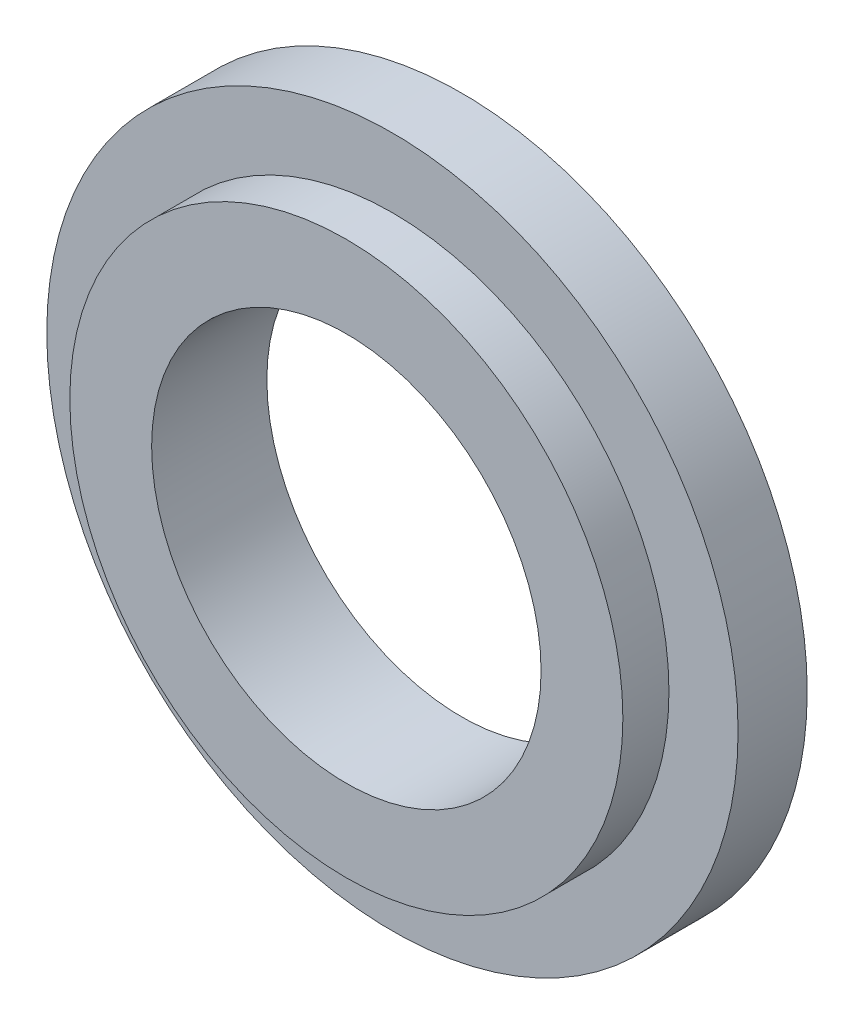
SolidWorks part; units mm, degrees
material "1023 Carbon Steel Sheet (SS)"
ref_plane "Front Plane" through (0, 0, 0) normal (0, 0, 1) x (1, 0, 0)
ref_plane "Top Plane" through (0, 0, 0) normal (0, 1, 0) x (1, 0, 0)
ref_plane "Right Plane" through (0, 0, 0) normal (1, 0, 0) x (0, 0, -1)
sketch "Sketch1" plane through (0, 0, 0) normal (0, 0, 1) x (1, 0, 0)
  circle A0 centre (0, 0) radius 15
  dimension "D1" = 30
extrude "Extrude1" add sketch "Sketch1" along normal blind 3
sketch "Sketch2" plane through (0, 0, 3) normal (0, 0, 1) x (1, 0, 0)
  circle A0 centre (0, 0) radius 12
  dimension "D1" = 24
extrude "Extrude2" add sketch "Sketch2" along normal blind 2
sketch "Sketch3" plane through (0, 0, 5) normal (0, 0, 1) x (1, 0, 0)
  circle A0 centre (0, 0) radius 8.45
  dimension "D1" = 16.9
extrude "Extrude3" cut sketch "Sketch3" against normal blind 13
